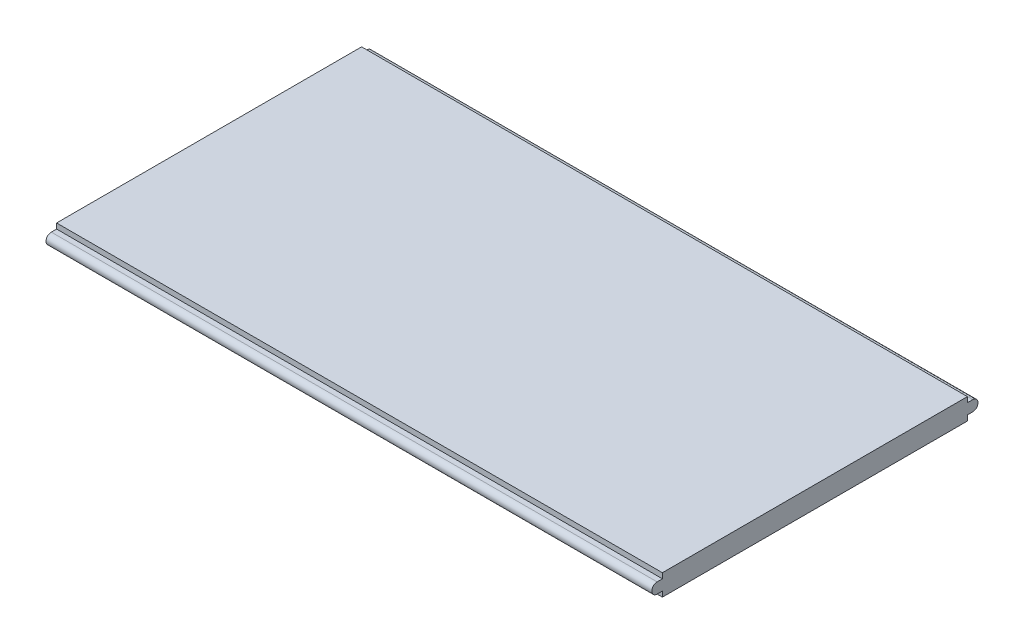
SolidWorks part; units mm, degrees
ref_plane "Front Plane" through (0, 0, 0) normal (0, 0, 1) x (1, 0, 0)
ref_plane "Top Plane" through (0, 0, 0) normal (0, 1, 0) x (1, 0, 0)
ref_plane "Right Plane" through (0, 0, 0) normal (1, 0, 0) x (0, 0, -1)
sketch "Sketch1" plane through (0, 0, 0) normal (1, 0, 0) x (0, 0, -1)
  line L0 (-372.5, 0) -> (-347.5, 0) construction
  line L1 (-360, 25) -> (360, 25)
  line L2 (-360, 25) -> (-360, -25)
  line L3 (-360, -25) -> (360, -25)
  line L4 (360, 25) -> (360, -25)
  line L5 (-360, 25) -> (360, -25) construction
  line L6 (-360, -25) -> (360, 25) construction
  line L7 (-372.5, 12.5) -> (-347.5, 12.5)
  line L8 (-372.5, -12.5) -> (-347.5, -12.5)
  line L9 (347.5, 0) -> (372.5, 0) construction
  line L10 (347.5, 12.5) -> (372.5, 12.5)
  line L11 (347.5, -12.5) -> (372.5, -12.5)
  arc A0 (-372.5, 12.5) -> (-372.5, -12.5) centre (-372.5, 0) ccw
  arc A1 (-347.5, -12.5) -> (-347.5, 12.5) centre (-347.5, 0) ccw
  arc A2 (347.5, 12.5) -> (347.5, -12.5) centre (347.5, 0) ccw
  arc A3 (372.5, -12.5) -> (372.5, 12.5) centre (372.5, 0) ccw
  point P0 (0, 0)
  point P8 (-360, 0)
  point P14 (360, 0)
  dimension "D1" = 720
  dimension "D2" = 50
  dimension "D3" = 25
  dimension "D4" = 25
  dimension "D5" = 25
  dimension "D6" = 25
extrude "Boss-Extrude1" add sketch "Sketch1" along normal blind 1430 contours A2 L10 L4 L1 L2 L7 A1 L8 L3 L11 | L8 A1 L7 L2 | L7 A0 L8 L2 | L11 A3 L10 L4 | L10 A2 L11 L4
